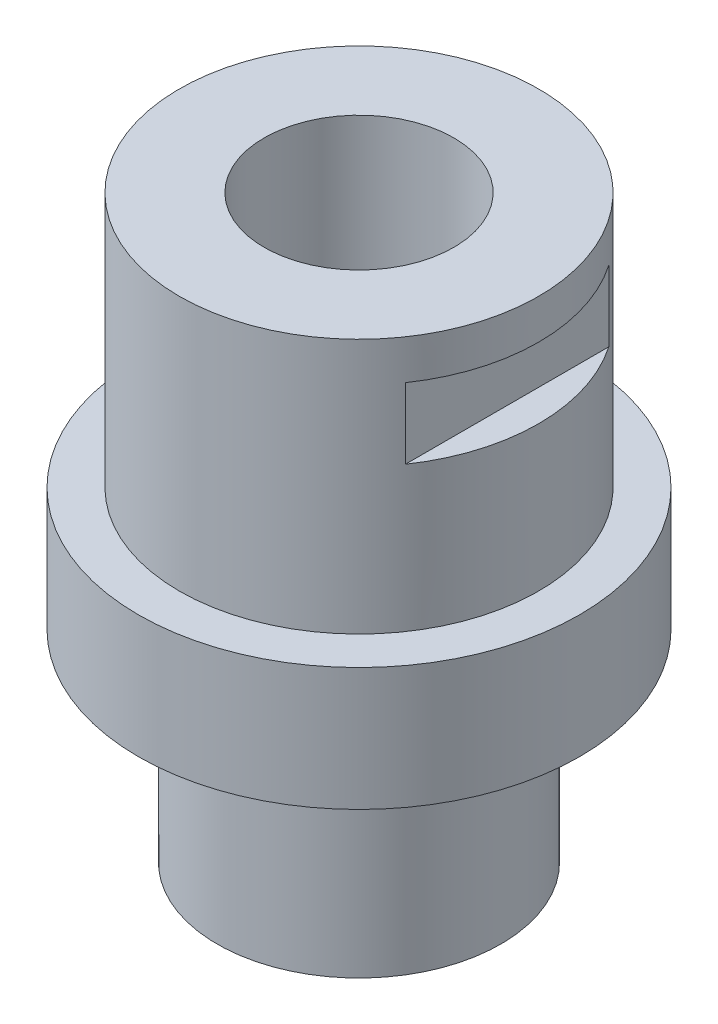
SolidWorks part; units mm, degrees
ref_plane "Front Plane" through (0, 0, 0) normal (0, 0, 1) x (1, 0, 0)
ref_plane "Top Plane" through (0, 0, 0) normal (0, 1, 0) x (1, 0, 0)
ref_plane "Right Plane" through (0, 0, 0) normal (1, 0, 0) x (0, 0, -1)
sketch "Sketch1" plane through (0, 0, 0) normal (0, 1, 0) x (1, 0, 0)
  circle A0 centre (0, 0) radius 35
extrude "Boss-Extrude1" add sketch "Sketch1" along normal blind 92 separate body
sketch "Sketch2" plane through (0, 92, 0) normal (0, 1, 0) x (1, 0, 0)
  circle A0 centre (0, 0) radius 28.5
extrude "Cut-Extrude1" cut sketch "Sketch2" against normal blind 40.5 flip side to cut
sketch "Sketch3" plane through (0, 0, 0) normal (0, -1, 0) x (1, 0, 0)
  circle A0 centre (0, 0) radius 22.5
extrude "Cut-Extrude2" cut sketch "Sketch3" against normal blind 32 flip side to cut
sketch "Sketch4" plane through (0, 0, 0) normal (0, -1, 0) x (1, 0, 0)
  circle A0 centre (0, 0) radius 15.05
extrude "Cut-Extrude3" cut sketch "Sketch4" against normal through all
sketch "Sketch5" plane through (0, 0, 0) normal (0, 0, 1) x (1, 0, 0)
  line L0 (28.5, 51.5) -> (28.5, 92) construction
  line L1 (23.5, 85.7) -> (28.5, 85.7)
  line L2 (23.5, 85.7) -> (23.5, 74.5)
  line L3 (23.5, 74.5) -> (28.5, 74.5)
  line L4 (28.5, 85.7) -> (28.5, 74.5)
extrude "TestingFeature" cut sketch "Sketch5" against normal through all both and the other way through all
mirror "Mirror1" about plane through (0, 0, 0) normal (1, 0, 0) of "TestingFeature"
